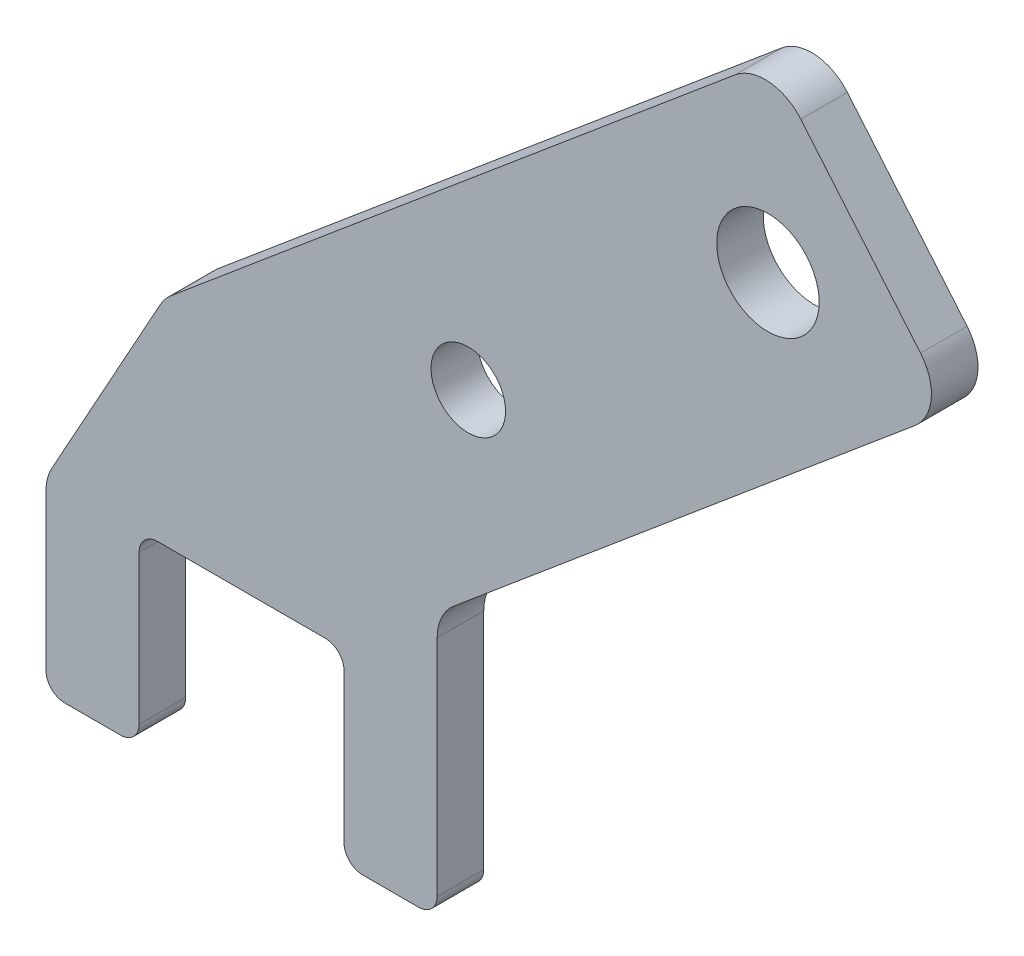
SolidWorks part; units mm, degrees
ref_plane "Plan de face" through (0, 0, 0) normal (0, 0, 1) x (1, 0, 0)
ref_plane "Plan de dessus" through (0, 0, 0) normal (0, 1, 0) x (1, 0, 0)
ref_plane "Plan de droite" through (0, 0, 0) normal (1, 0, 0) x (0, 0, -1)
sketch "Esquisse1" plane through (0, 0, 0) normal (0, 0, 1) x (1, 0, 0)
  line L1 (34.3978, 8.391) -> (89.5116, 54.6369)
  line L2 (89.5116, 54.6369) -> (70.2279, 77.6183)
  line L3 (70.2279, 77.6183) -> (5.1142, 22.9813)
  line L4 (79.8698, 66.1276) -> (0.437, -0.5243) construction
  line L5 (24.3978, 0) -> (5.1142, 22.9813) construction
  line L6 (24.3978, 0) -> (24.3978, -20)
  line L7 (24.3978, -20) -> (34.3978, -20)
  line L8 (34.3978, -20) -> (34.3978, 8.391)
  line L9 (2.3978, 0) -> (2.3978, -20)
  line L10 (2.3978, -20) -> (-7.6022, -20)
  line L11 (-7.6022, -20) -> (-7.6022, 0)
  line L12 (2.3978, 0) -> (24.3978, 0)
  line L13 (34.3978, 8.391) -> (24.3978, 0) construction
  line L14 (-7.6022, 0) -> (5.1142, 22.9813)
  circle A0 centre (69.9112, 57.7714) radius 5.5
  circle A1 centre (37.7373, 30.7743) radius 4
  point P11 (14.756, 11.4907)
  dimension "D5" = 11
  dimension "D6" = 8
  dimension "D1" = 30
  dimension "D2" = 85
  dimension "D3" = 30
  dimension "D4" = 72
  dimension "D7" = 40
  dimension "D8" = 22
  dimension "D9" = 10
  dimension "D10" = 10
  dimension "D11" = 20
extrude "Boss.-Extru.1" add sketch "Esquisse1" along normal blind 5
fillet "Congé1" radius 5 5 edges at (34.3978, 8.391, 2.5) (-7.6022, 0, 2.5) (5.1142, 22.9813, 2.5) (89.5116, 54.6369, 2.5) (70.2279, 77.6183, 2.5)
fillet "Congé2" radius 2 6 edges at (34.3978, -20, 2.5) (24.3978, -20, 2.5) (24.3978, 0, 2.5) (2.3978, 0, 2.5) (2.3978, -20, 2.5) (-7.6022, -20, 2.5)
